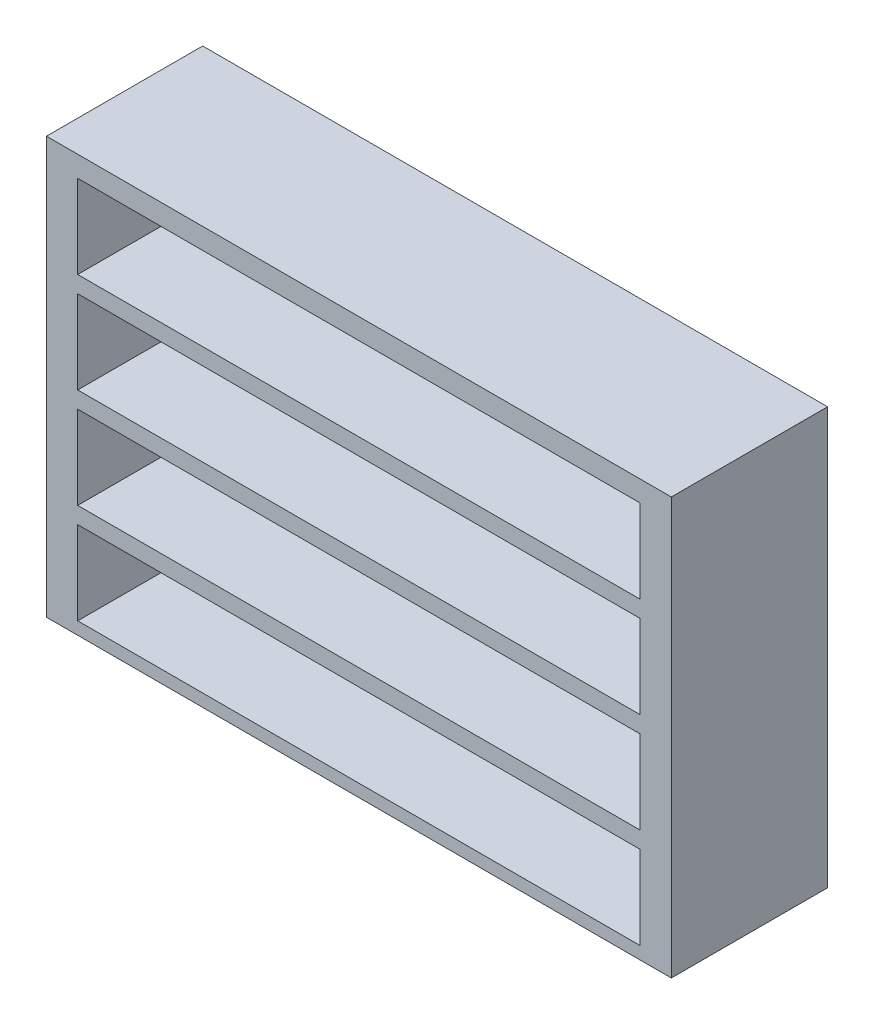
SolidWorks part; units mm, degrees
ref_plane "Front Plane" through (0, 0, 0) normal (0, 0, 1) x (1, 0, 0)
ref_plane "Top Plane" through (0, 0, 0) normal (0, 1, 0) x (1, 0, 0)
ref_plane "Right Plane" through (0, 0, 0) normal (1, 0, 0) x (0, 0, -1)
sketch "Sketch1" plane through (0, 0, 0) normal (0, 0, 1) x (1, 0, 0)
  line L1 (-1500, -1000) -> (1500, -1000)
  line L2 (-1500, -1000) -> (-1500, 1000)
  line L3 (-1500, 1000) -> (1500, 1000)
  line L4 (1500, -1000) -> (1500, 1000)
  line L5 (-1500, -1000) -> (1500, 1000) construction
  line L6 (-1500, 1000) -> (1500, -1000) construction
  point P0 (0, 0)
  dimension "D1" = 3000
  dimension "D2" = 2000
extrude "Boss-Extrude1" add sketch "Sketch1" along normal blind 750
sketch "Sketch2" plane through (0, 0, 750) normal (0, 0, 1) x (1, 0, 0)
  line L0 (0, 0) -> (0, 268.145) construction
  line L1 (-1350, 900) -> (1350, 900)
  line L2 (-1350, 900) -> (-1350, 500)
  line L3 (-1350, 500) -> (1350, 500)
  line L4 (1350, 900) -> (1350, 500)
  line L5 (1500, 1000) -> (-1500, 1000) construction
  dimension "D1" = 2700
  dimension "D2" = 100
  dimension "D3" = 400
extrude "Cut-Extrude1" cut sketch "Sketch2" against normal blind 725
pattern_linear "LPattern1" count 4 spacing 480 along (0, -1, 0) of "Cut-Extrude1"
